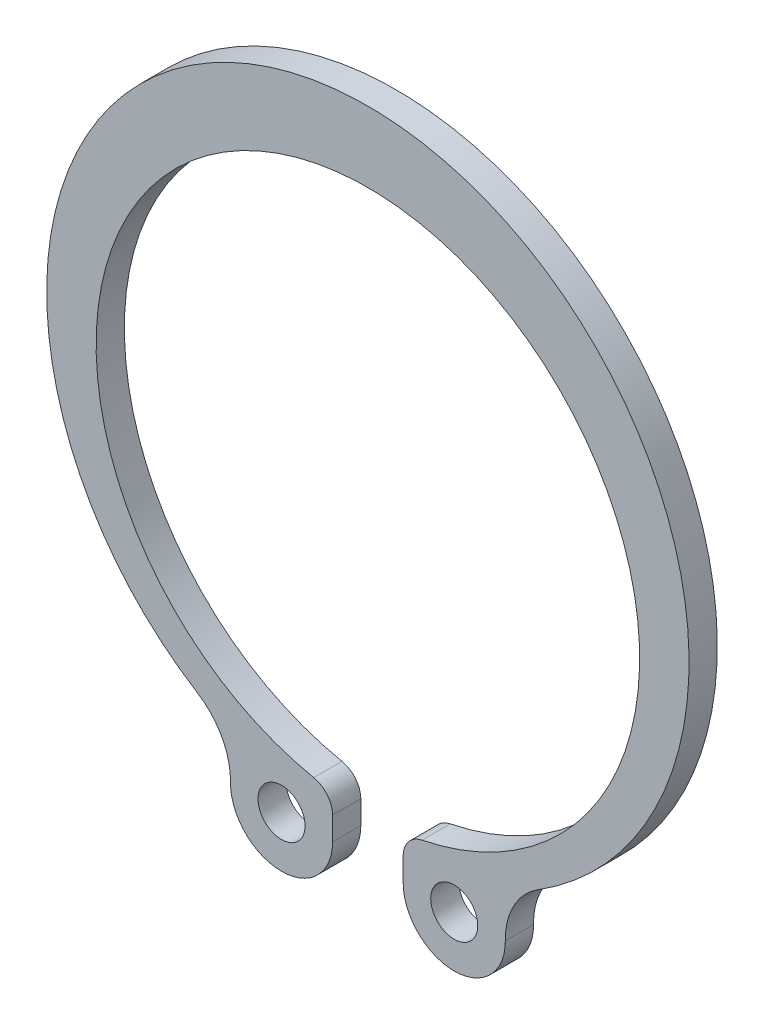
SolidWorks part; units mm, degrees
material "AISI Тип A2 Инструментальная сталь"
ref_plane "Спереди" through (0, 0, 0) normal (0, 0, 1) x (1, 0, 0)
ref_plane "Сверху" through (0, 0, 0) normal (0, 1, 0) x (1, 0, 0)
ref_plane "Справа" through (0, 0, 0) normal (1, 0, 0) x (0, 0, -1)
sketch "Эскиз1" plane through (0, 0, 0) normal (0, 0, 1) x (1, 0, 0)
  line L0 (0, -1000) -> (0, 49000) construction
  line L1 (-1.5, -14.183) -> (-1.5, -13.1985)
  line L2 (1.5, -14.183) -> (1.5, -13.1985)
  arc A0 (7.2459, -11.568) -> (-7.2459, -11.568) centre (0, 0) ccw
  arc A1 (2.3008, -12.2185) -> (-2.3008, -12.2185) centre (0, -0.9) ccw
  circle A2 centre (-3.6695, -14.183) radius 1
  arc A3 (-5.8387, -14.1526) -> (-1.5, -14.183) centre (-3.6695, -14.183) ccw
  arc A4 (-2.3008, -12.2185) -> (-1.5, -13.1985) centre (-2.5, -13.1985) cw
  arc A5 (-7.2459, -11.568) -> (-5.8387, -14.1526) centre (-8.8384, -14.1104) cw
  arc A6 (7.2459, -11.568) -> (5.8387, -14.1526) centre (8.8384, -14.1104) ccw
  arc A7 (2.3008, -12.2185) -> (1.5, -13.1985) centre (2.5, -13.1985) ccw
  arc A8 (5.8387, -14.1526) -> (1.5, -14.183) centre (3.6695, -14.183) cw
  circle A9 centre (3.6695, -14.183) radius 1
  point P12 (0, 0)
  point P17 (-1.5, -12.3522)
  dimension "D2" = 27.3
  dimension "D3" = 23.1
  dimension "D4" = 2
  dimension "D5" = 1
  dimension "D6" = 3
  dimension "D7" = 3
  dimension "D8" = 4.4
  dimension "D1" = 0.9
extrude "Бобышка-Вытянуть1" add sketch "Эскиз1" along normal blind 1.2
